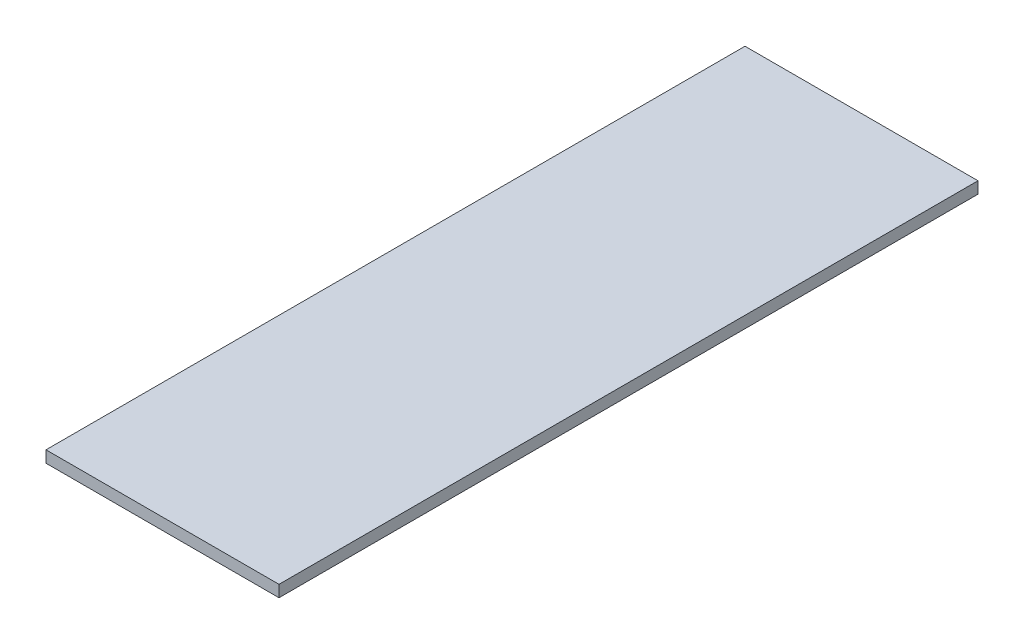
SolidWorks part; units mm, degrees
material "6061 Alloy"
ref_plane "Front Plane" through (0, 0, 0) normal (0, 0, 1) x (1, 0, 0)
ref_plane "Top Plane" through (0, 0, 0) normal (0, 1, 0) x (1, 0, 0)
ref_plane "Right Plane" through (0, 0, 0) normal (1, 0, 0) x (0, 0, -1)
sketch "Sketch1" plane through (0, 0, 0) normal (0, 1, 0) x (1, 0, 0)
  line L1 (-50, -150) -> (50, -150)
  line L2 (-50, -150) -> (-50, 150)
  line L3 (-50, 150) -> (50, 150)
  line L4 (50, -150) -> (50, 150)
  line L5 (-50, -150) -> (50, 150) construction
  line L6 (-50, 150) -> (50, -150) construction
  point P0 (0, 0)
  dimension "D1" = 100
  dimension "D2" = 300
extrude "Boss-Extrude1" add sketch "Sketch1" along normal blind 5
